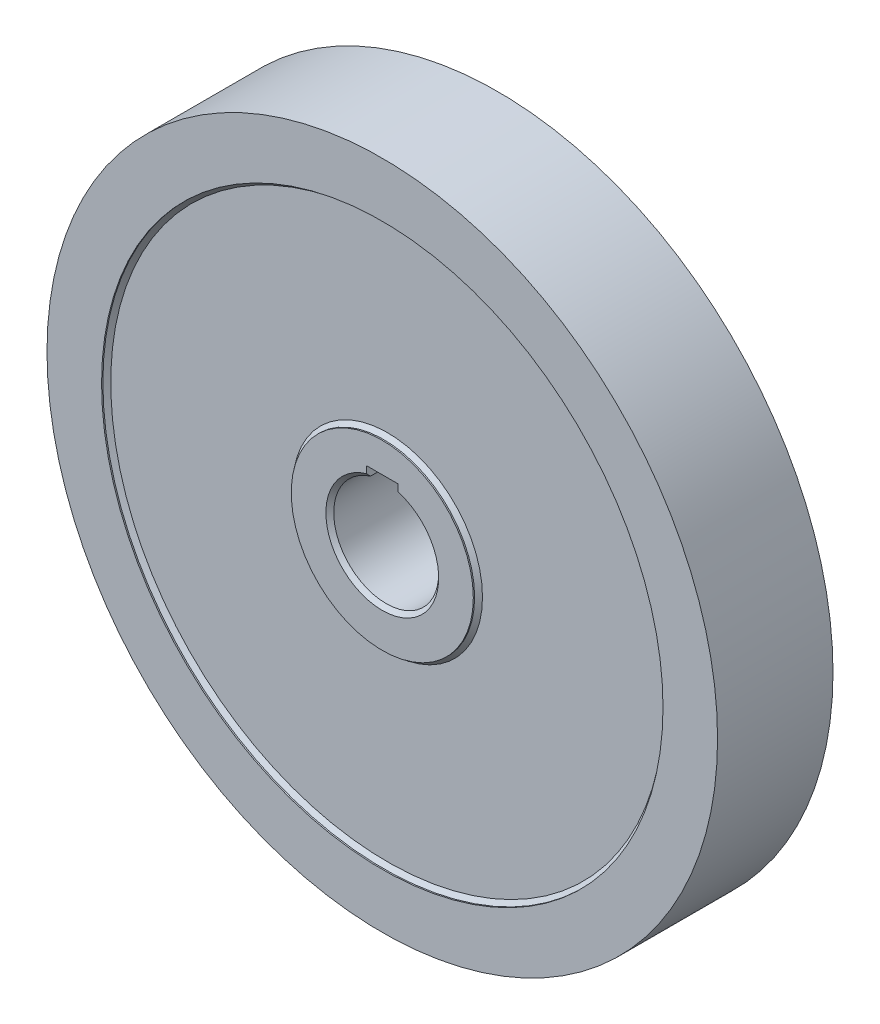
SolidWorks part; units mm, degrees
ref_plane "Front Plane" through (0, 0, 0) normal (0, 0, 1) x (1, 0, 0)
ref_plane "Top Plane" through (0, 0, 0) normal (0, 1, 0) x (1, 0, 0)
ref_plane "Right Plane" through (0, 0, 0) normal (1, 0, 0) x (0, 0, -1)
sketch "Sketch3" plane through (0, 0, 0) normal (0, 0, 1) x (1, 0, 0)
  circle A0 centre (0, 0) radius 127.8
  dimension "D1" = 255.6
extrude "Boss-Extrude1" add sketch "Sketch3" along normal mid plane 44
sketch "Sketch6" plane through (0, 0, 22) normal (0, 0, 1) x (1, 0, 0)
  line L2 (-6, 19.0788) -> (-6, 23.3)
  line L3 (-6, 23.3) -> (6, 23.3)
  line L4 (6, 19.0788) -> (6, 23.3)
  arc A0 (-6, 19.0788) -> (6, 19.0788) centre (0, 0) ccw
  point P3 (0, 20)
  dimension "D1" = 40
  dimension "D3" = 12
extrude "Cut-Extrude1" cut sketch "Sketch6" against normal through all both and the other way through all
sketch "Sketch7" plane through (0, 0, 22) normal (0, 0, 1) x (1, 0, 0)
  circle A0 centre (0, 0) radius 107
  circle A2 centre (0, 0) radius 34.7
  dimension "D1" = 214
  dimension "D2" = 69.4
extrude "Cut-Extrude2" cut sketch "Sketch7" against normal blind 2
mirror "Mirror1" about plane through (0, 0, 0) normal (0, 0, 1) of "Cut-Extrude2"
chamfer "Chamfer1" distance 1.5 angle 45 1 edges at (107, 0, 20)
chamfer "Chamfer2" distance 1.5 angle 45 1 edges at (34.7, 0, 20)
chamfer "Chamfer3" distance 1.5 angle 45 1 edges at (0, -20, 22)
chamfer "Chamfer4" distance 1.5 angle 45 3 edges at (0, -20, -22) (34.7, 0, -20) (107, 0, -20)
sketch "Sketch10" plane through (0, 0, 22) normal (0, 0, 1) x (1, 0, 0)
  line L0 (0, 0) -> (0, 127.8) construction
  line L1 (6, 19.0788) -> (6, 136.3918) construction
  line L3 (-6, 23.3) -> (-6, 136.3918) construction
  circle A0 centre (0, 0) radius 119.9
  circle A1 centre (0, 0) radius 124.25
  circle A2 centre (0, 0) radius 127.8 construction
  dimension "D1" = 248.5
